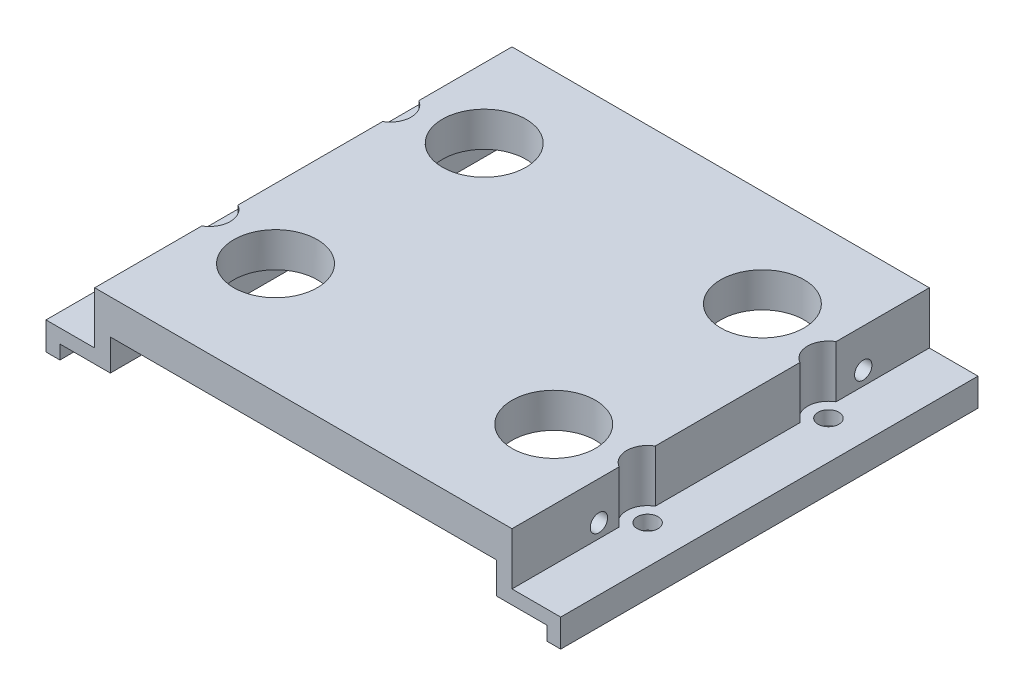
SolidWorks part; units mm, degrees
ref_plane "Front Plane" through (0, 0, 0) normal (0, 0, 1) x (1, 0, 0)
ref_plane "Top Plane" through (0, 0, 0) normal (0, 1, 0) x (1, 0, 0)
ref_plane "Right Plane" through (0, 0, 0) normal (1, 0, 0) x (0, 0, -1)
sketch "Sketch1" plane through (0, 0, 0) normal (0, 0, 1) x (1, 0, 0)
  line L0 (0, 0) -> (0, -2)
  line L1 (0, -2) -> (-2, -2)
  line L2 (-2, -2) -> (-2, 2)
  line L3 (-2, 2) -> (5, 2)
  line L4 (5, 2) -> (5, 9.5)
  line L5 (5, 9.5) -> (65, 9.5)
  line L6 (65, 9.5) -> (65, 2)
  line L7 (65, 2) -> (72, 2)
  line L8 (72, 2) -> (72, -2)
  line L9 (72, -2) -> (70, -2)
  line L10 (70, -2) -> (70, 0)
  line L11 (70, 0) -> (62.75, 0)
  line L12 (62.75, 0) -> (62.75, 4.5)
  line L13 (62.75, 4.5) -> (7.25, 4.5)
  line L14 (7.25, 4.5) -> (7.25, 0)
  line L15 (7.25, 0) -> (0, 0)
  line L16 (7.25, 0) -> (62.75, 0) construction
  line L17 (0, -2) -> (70, -2) construction
  point P17 (35, 0)
  point P18 (35, -2)
  point P21 (35, 9.5)
  dimension "D1" = 55.5
  dimension "D2" = 70
  dimension "D3" = 4.5
  dimension "D4" = 5
  dimension "D5" = 2
  dimension "D6" = 60
  dimension "D7" = 2
  dimension "D8" = 2
extrude "Boss-Extrude1" add sketch "Sketch1" along normal mid plane 60
sketch "Sketch3" plane through (5, 0, 0) normal (-1, 0, 0) x (0, 0, 1)
  line L0 (30, 2) -> (-30, 2) construction
  circle A0 centre (-20.499, 4) radius 1.5
  circle A1 centre (17.501, 4) radius 1.5
  point P7 (17.501, 4)
  point P8 (-20.499, 4)
  dimension "D2" = 2
  dimension "D3" = 3
  dimension "D1" = 38
sketch "Sketch5" plane through (65, 0, 0) normal (1, 0, 0) x (0, 0, -1)
  point P0 (-17.501, 4)
  point P1 (20.499, 4)
hole_wizard "M3 Tapped Hole1" positions "3DSketch1" profile "Sketch6" tap size "M3" standard "ISO"
sketch3d "3DSketch1"
  point P0 (5, 4, 17.501)
  point P3 (5, 4, -20.499)
  point P6 (65, 4, 17.501)
  point P9 (65, 4, -20.499)
sketch "Sketch6" plane through (5, 4, 17.501) normal (0, 1, 0) x (0, 0, 1)
  line L0 (0, 0) -> (0, 5.7511)
  line L1 (0, 5.7511) -> (1.25, 5)
  line L2 (1.25, 5) -> (1.25, 0)
  line L5 (1.25, 0) -> (0, 0)
  line L10 (0, 5.7511) -> (-1.25, 5) construction
  line L11 (0, -6.35) -> (0, 107.95) construction
  dimension "Tap Drill Dia." = 2.5
  dimension "Tap Drill Depth" = 5
  dimension "Drill Angle" = 118
cosmetic thread "Hole Thread1" parameters "D1"=6, "D2"=3
cosmetic thread "Hole Thread2" parameters "D1"=6, "D2"=3
cosmetic thread "Hole Thread3" parameters "D1"=6, "D2"=3
cosmetic thread "Hole Thread4" parameters "D1"=6, "D2"=3
sketch "Sketch7" plane through (0, 2, 0) normal (0, 1, 0) x (1, 0, 0)
  line L0 (3.5, 14) -> (66.5, -12) construction
  line L1 (3.5, 14) -> (66.5, 14) construction
  line L2 (3.5, 14) -> (3.5, -12) construction
  line L3 (3.5, -12) -> (66.5, -12) construction
  line L4 (66.5, 14) -> (66.5, -12) construction
  line L5 (35, -30) -> (35, 1) construction
  line L6 (65, -30) -> (5, -30) construction
  circle A0 centre (3.5, 14) radius 1.5
  circle A1 centre (66.5, 14) radius 1.5
  circle A2 centre (3.5, -12) radius 1.5
  circle A3 centre (66.5, -12) radius 1.5
  dimension "D3" = 3
  dimension "D1" = 26
  dimension "D2" = 63
  dimension "D4" = 31
extrude "Cut-Extrude2" cut sketch "Sketch7" against normal through all
sketch "Sketch8" plane through (0, 9.5, 0) normal (0, 1, 0) x (1, 0, 0)
  circle A0 centre (3.5, 14) radius 3
  circle A1 centre (3.5, -12) radius 3
  circle A2 centre (66.5, 14) radius 3
  circle A3 centre (66.5, -12) radius 3
  dimension "D1" = 6
extrude "Cut-Extrude3" cut sketch "Sketch8" against normal up to surface (7.5 mm away) up to face at (2.5, 2, -0.5)
sketch "Sketch2" plane through (0, 9.5, 0) normal (0, 1, 0) x (1, 0, 0)
  line L0 (35, 16) -> (35, 30) construction
  line L1 (15, 16) -> (55, 16) construction
  line L2 (15, 16) -> (15, -14) construction
  line L3 (15, -14) -> (55, -14) construction
  line L4 (55, 16) -> (55, -14) construction
  line L5 (15, 16) -> (55, -14) construction
  line L6 (15, -14) -> (55, 16) construction
  line L7 (3.5, 14) -> (3.5, -12) construction
  line L8 (65, 30) -> (5, 30) construction
  line L9 (3.5, 1) -> (15, 1) construction
  circle A0 centre (15, 16) radius 6
  circle A1 centre (55, 16) radius 6
  circle A2 centre (15, -14) radius 6
  circle A3 centre (55, -14) radius 6
  point P0 (35, 1)
  dimension "D3" = 12
  dimension "D1" = 30
  dimension "D2" = 40
extrude "Cut-Extrude1" cut sketch "Sketch2" against normal through all
